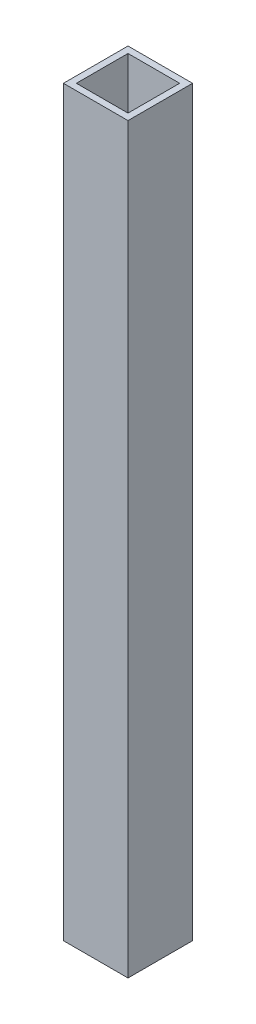
SolidWorks part; units mm, degrees
material "AISI 1020"
ref_plane "Front Plane" through (0, 0, 0) normal (0, 0, 1) x (1, 0, 0)
ref_plane "Top Plane" through (0, 0, 0) normal (0, 1, 0) x (1, 0, 0)
ref_plane "Right Plane" through (0, 0, 0) normal (1, 0, 0) x (0, 0, -1)
sketch "Sketch1" plane through (0, 0, 0) normal (0, 0, 1) x (1, 0, 0)
  line L1 (-31.7391, 49.7826) -> (-11.7391, 49.7826)
  line L2 (-31.7391, 49.7826) -> (-31.7391, -180.2174)
  line L3 (-31.7391, -180.2174) -> (-11.7391, -180.2174)
  line L4 (-11.7391, 49.7826) -> (-11.7391, -180.2174)
  dimension "D1" = 20
  dimension "D2" = 230
extrude "Boss-Extrude1" add sketch "Sketch1" against normal blind 20
sketch "Sketch2" plane through (0, 49.7826, 0) normal (0, 1, 0) x (1, 0, 0)
  line L8 (-29.7391, 2) -> (-13.7391, 2)
  line L9 (-13.7391, 2) -> (-13.7391, 18)
  line L10 (-13.7391, 18) -> (-29.7391, 18)
  line L11 (-29.7391, 18) -> (-29.7391, 2)
  line L12 (-29.7391, 2) -> (-13.7391, 2)
  line L13 (-13.7391, 2) -> (-13.7391, 18)
  line L14 (-13.7391, 18) -> (-29.7391, 18)
  line L15 (-29.7391, 18) -> (-29.7391, 2)
  dimension "D1" = 2
extrude "Cut-Extrude1" cut sketch "Sketch2" against normal blind 200
